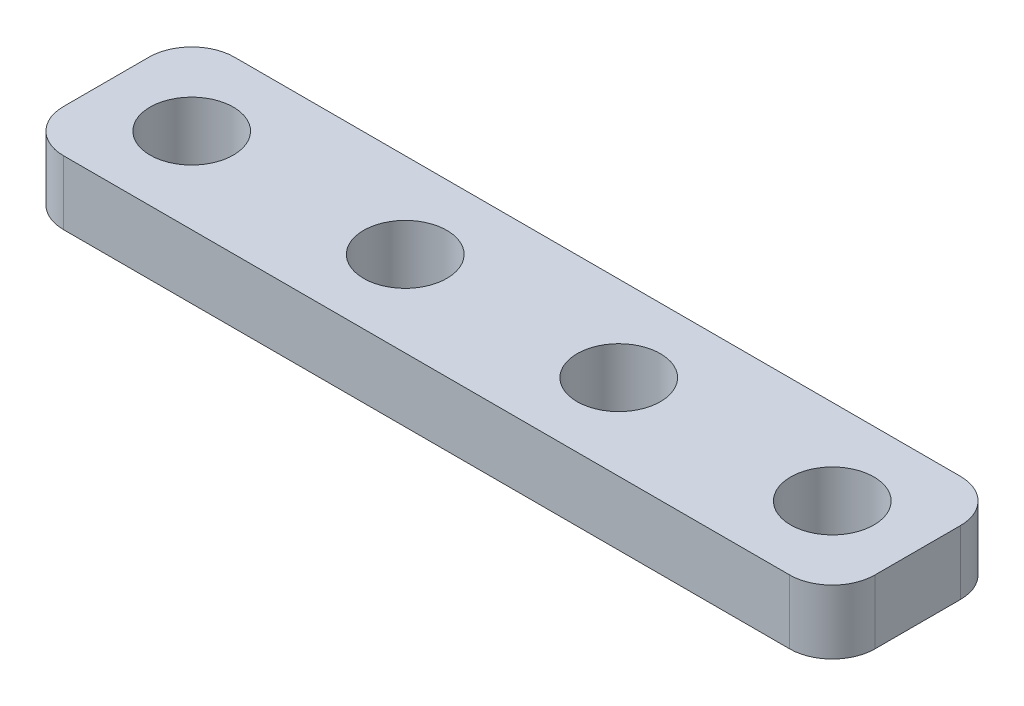
SolidWorks part; units mm, degrees
ref_plane "Front Plane" through (0, 0, 0) normal (0, 0, 1) x (1, 0, 0)
ref_plane "Top Plane" through (0, 0, 0) normal (0, 1, 0) x (1, 0, 0)
ref_plane "Right Plane" through (0, 0, 0) normal (1, 0, 0) x (0, 0, -1)
sketch "Sketch1" plane through (0, 0, 0) normal (0, 1, 0) x (1, 0, 0)
  line L1 (2, 0) -> (36, 0)
  line L2 (0, -2) -> (0, -6)
  line L3 (2, -8) -> (36, -8)
  line L4 (38, -2) -> (38, -6)
  arc A0 (36, -8) -> (38, -6) centre (36, -6) ccw
  arc A1 (0, -6) -> (2, -8) centre (2, -6) ccw
  arc A2 (2, 0) -> (0, -2) centre (2, -2) ccw
  arc A3 (36, 0) -> (38, -2) centre (36, -2) cw
  point P7 (38, -8)
  point P12 (0, 0)
  point P15 (38, 0)
  dimension "D3" = 2
  dimension "D1" = 38
  dimension "D2" = 8
extrude "Boss-Extrude1" add sketch "Sketch1" along normal blind 3
sketch "Sketch2" plane through (0, 3, 0) normal (0, 1, 0) x (1, 0, 0)
  line L2 (34, -4) -> (-16, -4) construction
  line L4 (38, -6) -> (38, -2) construction
  line L7 (36, 0) -> (2, 0) construction
  circle A16 centre (34, -4) radius 1.95
  circle A17 centre (24, -4) radius 1.95
  circle A18 centre (14, -4) radius 1.95
  circle A19 centre (-16, -4) radius 1.95
  circle A20 centre (4, -4) radius 1.95
  circle A21 centre (-6, -4) radius 1.95
  dimension "D1" = 10
  dimension "D4" = 3.9
  dimension "D7" = 3.9
  dimension "D8" = 3.9
  dimension "D9" = 10
  dimension "D10" = 10
  dimension "D11" = 10
  dimension "D12" = 4
  dimension "D13" = 4
  dimension "D6" = 3.9
  dimension "D5" = 3.9
  dimension "D3" = 3.9
  dimension "D2" = 10
extrude "Cut-Extrude1" cut sketch "Sketch2" against normal through all
